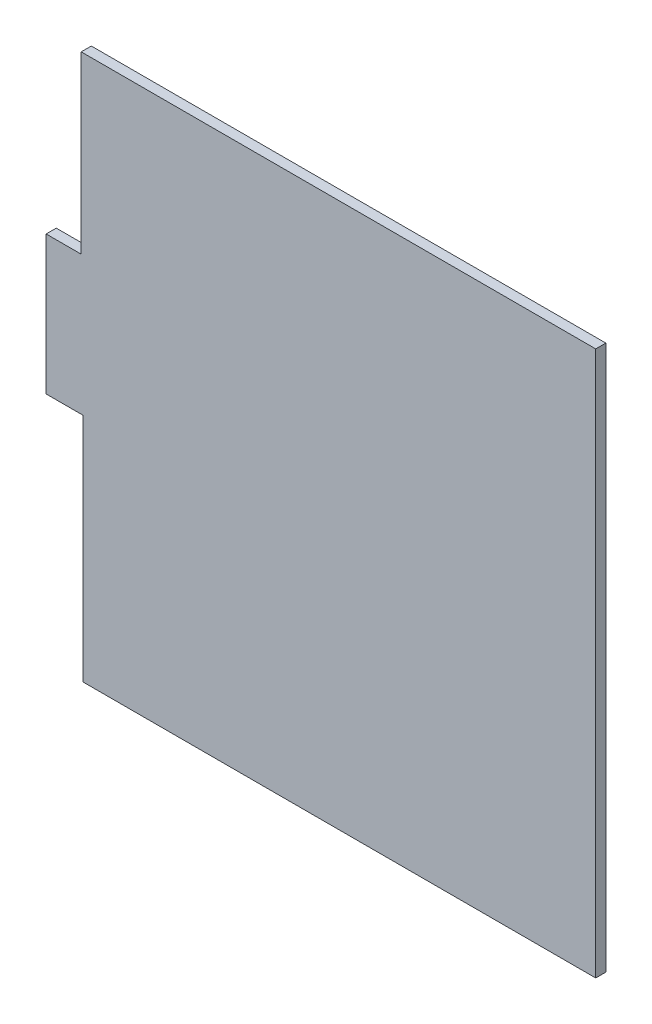
SolidWorks part; units mm, degrees
material "Cedar"
ref_plane "Front Plane" through (0, 0, 0) normal (0, 0, 1) x (1, 0, 0)
ref_plane "Top Plane" through (0, 0, 0) normal (0, 1, 0) x (1, 0, 0)
ref_plane "Right Plane" through (0, 0, 0) normal (1, 0, 0) x (0, 0, -1)
sketch "Model" plane through (0, 0, 0) normal (0, 0, 1) x (1, 0, 0)
  line L0 (731.3204, 258.0659) -> (409.3204, 258.0659)
  line L1 (731.3204, 258.0659) -> (731.3204, 600.0659)
  line L2 (731.3204, 600.0659) -> (408.3204, 600.0659)
  line L3 (408.3204, 600.0659) -> (408.3204, 490.0659)
  line L4 (408.3204, 490.0659) -> (386.3204, 490.0659)
  line L5 (409.3204, 403.0659) -> (409.3204, 258.0659)
  line L6 (409.3204, 403.0659) -> (386.3204, 403.0659)
  line L7 (386.3204, 403.0659) -> (386.3204, 490.0659)
  circle A0 centre (396.3204, 472.6874) radius 2.5
  circle A1 centre (396.3204, 450.6874) radius 2.5
  circle A2 centre (396.3204, 425.6874) radius 2.5
  circle A3 centre (491.3204, 441.6874) radius 2.5
  circle A4 centre (561.3204, 441.6874) radius 2.5
  circle A5 centre (641.3204, 441.6874) radius 2.5
  circle A6 centre (681.8766, 506.2088) radius 2.5
  circle A7 centre (681.8766, 366.2088) radius 2.5
  circle A8 centre (461.8766, 366.2088) radius 2.5
  circle A9 centre (461.8766, 506.2088) radius 2.5
extrude "Boss-Extrude1" add sketch "Model" against normal blind 6.35 contours L3 L4 L7 L6 L5 L0 L1 L2
